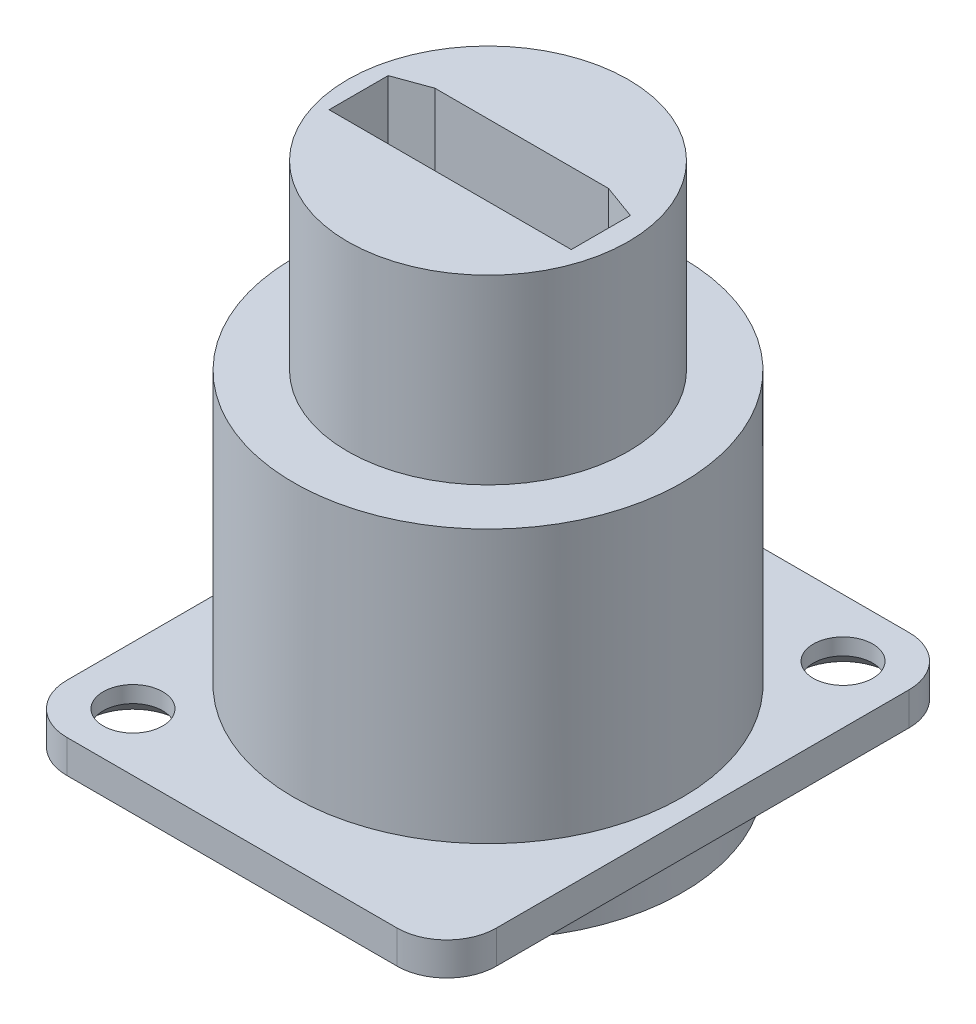
SolidWorks part; units mm, degrees
ref_plane "Спереди" through (0, 0, 0) normal (0, 0, 1) x (1, 0, 0)
ref_plane "Сверху" through (0, 0, 0) normal (0, 1, 0) x (1, 0, 0)
ref_plane "Справа" through (0, 0, 0) normal (1, 0, 0) x (0, 0, -1)
sketch "Sketch1" plane through (0, 0, 0) normal (0, 1, 0) x (1, 0, 0)
  line L1 (0, 0) -> (26, 0)
  line L2 (0, 0) -> (0, -31)
  line L3 (0, -31) -> (26, -31)
  line L4 (26, 0) -> (26, -31)
  dimension "D1" = 31
  dimension "D2" = 26
extrude "Extrude1" add sketch "Sketch1" along normal blind 2
sketch "Sketch2" plane through (0, 0, 0) normal (0, -1, 0) x (-1, 0, 0)
  line L0 (-13, -31) -> (-13, 0) construction
  line L1 (0, -31) -> (-26, -31) construction
  line L2 (-26, 0) -> (0, 0) construction
  line L3 (0, -15.5) -> (-26, -15.5) construction
  line L4 (0, 0) -> (0, -31) construction
  line L5 (-26, -31) -> (-26, 0) construction
  circle A0 centre (-13, -15.5) radius 11.775
  dimension "D1" = 23.55
extrude "Extrude2" add sketch "Sketch2" along normal blind 3 and the other way blind 18.5
sketch "Sketch3" plane through (0, 18.5, 0) normal (0, 1, 0) x (1, 0, 0)
  circle A0 centre (13, -15.5) radius 8.5
  dimension "D1" = 17
extrude "Extrude3" add sketch "Sketch3" along normal blind 11
sketch "Sketch4" plane through (0, -3, 0) normal (0, -1, 0) x (-1, 0, 0)
  circle A0 centre (-13, -15.5) radius 8.5
  circle A1 centre (-13, -15.5) radius 10
  dimension "D1" = 17
  dimension "D2" = 20
extrude "Extrude4" cut sketch "Sketch4" against normal blind 15
sketch "Sketch5" plane through (0, -3, 0) normal (0, -1, 0) x (-1, 0, 0)
  line L0 (-5.5193, -14.0655) -> (-7.5967, -13.3094)
  line L1 (-5.5193, -17.6439) -> (-20.1871, -17.6439)
  line L2 (-5.5193, -17.6439) -> (-5.5193, -14.0655)
  line L4 (-20.1871, -17.6439) -> (-20.1871, -14.0655)
  line L5 (-7.5967, -13.3094) -> (-18.1097, -13.3094)
  line L6 (-18.1097, -13.3094) -> (-20.1871, -14.0655)
  dimension "D1" = 3.5784
  dimension "D2" = 14.6678
  dimension "D3" = 110
  dimension "D4" = 110
extrude "Extrude5" cut sketch "Sketch5" against normal blind 10
sketch "Sketch9" plane through (0, 0, 0) normal (0, -1, 0) x (1, 0, 0)
  line L0 (0, 15.5) -> (25.6067, 15.5) construction
  line L1 (0, 0) -> (0, 31) construction
  line L2 (13, 15.5) -> (13, 33.0737) construction
  circle A0 centre (3.5, 27.5) radius 1.8
  circle A1 centre (22.5, 3.5) radius 1.8
  dimension "D1" = 3.6
  dimension "D2" = 3.6
  dimension "D3" = 19
  dimension "D4" = 9.5
  dimension "D5" = 24
  dimension "D6" = 12
extrude "Extrude6" cut sketch "Sketch9" against normal blind 10
chamfer "Chamfer1" distance 1 angle 45 2 edges at (22.5, 0, 1.7) (3.5, 0, 25.7)
fillet "Fillet1" radius 3 4 edges at (26, 1, 31) (0, 1, 31) (0, 1, 0) (26, 1, 0)
sketch "Sketch10" plane through (0, 29.5, 0) normal (0, 1, 0) x (1, 0, 0)
  line L6 (5.5193, -14.0655) -> (5.5193, -17.6439)
  line L7 (7.5967, -13.3094) -> (5.5193, -14.0655)
  line L8 (18.1097, -13.3094) -> (7.5967, -13.3094)
  line L9 (20.1871, -14.0655) -> (18.1097, -13.3094)
  line L10 (20.1871, -17.6439) -> (20.1871, -14.0655)
  line L11 (5.5193, -17.6439) -> (20.1871, -17.6439)
  line L12 (5.5193, -14.0655) -> (5.5193, -17.6439)
  line L13 (7.5967, -13.3094) -> (5.5193, -14.0655)
  line L14 (18.1097, -13.3094) -> (7.5967, -13.3094)
  line L15 (20.1871, -14.0655) -> (18.1097, -13.3094)
  line L16 (20.1871, -17.6439) -> (20.1871, -14.0655)
  line L17 (5.5193, -17.6439) -> (20.1871, -17.6439)
  dimension "D1" = 0
extrude "Extrude7" cut sketch "Sketch10" against normal blind 10
